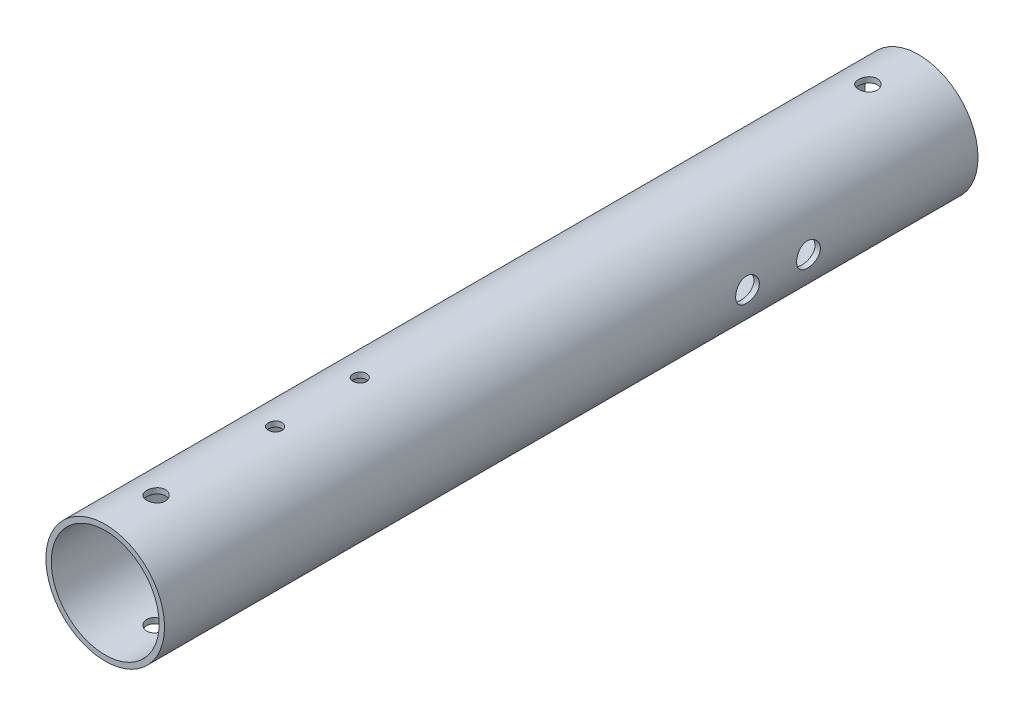
SolidWorks part; units mm, degrees
material "1060 Alloy"
ref_plane "Front Plane" through (0, 0, 0) normal (0, 0, 1) x (1, 0, 0)
ref_plane "Top Plane" through (0, 0, 0) normal (0, 1, 0) x (1, 0, 0)
ref_plane "Right Plane" through (0, 0, 0) normal (1, 0, 0) x (0, 0, -1)
sketch "Sketch2" plane through (0, 0, 0) normal (0, 0, 1) x (1, 0, 0)
  circle A0 centre (0, 0) radius 17.5
  circle A1 centre (0, 0) radius 15.9125
  dimension "D1" = 35
  dimension "D2" = 31.825
extrude "Boss-Extrude1" add sketch "Sketch2" along normal mid plane 240
sketch "Sketch4" plane through (0, 0, 0) normal (0, 1, 0) x (1, 0, 0)
  line L0 (0, 120) -> (0, 105) construction
  line L1 (15.9125, 120) -> (-15.9125, 120) construction
  dimension "D1" = 15
hole_wizard "M5 Clearance Hole1" positions "Sketch5" profile "Sketch6" hole size "M5" standard "AS"
sketch "Sketch5" plane through (0, 0, 0) normal (0, 1, 0) x (1, 0, 0)
  point P0 (0, 105)
sketch "Sketch6" plane through (0, 0, -105) normal (1, 0, 0) x (0, 0, -1)
  line L0 (0, 0) -> (0, 17.5)
  line L1 (0, 17.5) -> (2.75, 17.5)
  line L2 (2.75, 17.5) -> (2.75, 0)
  line L5 (2.75, 0) -> (0, 0)
  line L11 (0, -6.35) -> (0, 107.95) construction
  dimension "Thru Hole Dia." = 5.5
  dimension "Thru Hole Depth" = 17.5
mirror "Mirror1" about plane through (0, 0, 0) normal (0, 0, 1) of "M5 Clearance Hole1" second plane through (0, 0, 0) second plane normal (0, 1, 0)
sketch "Sketch7" plane through (0, 0, 0) normal (1, 0, 0) x (0, 0, -1)
  line L0 (52, 0) -> (70, 0) construction
  line L1 (70, 0) -> (120, 0) construction
  line L2 (120, -17.5) -> (120, 17.5) construction
  circle A0 centre (52, 0) radius 3.5
  circle A1 centre (70, 0) radius 3.5
  point P0 (70, 0)
  point P1 (52, 0)
  dimension "D3" = 7
  dimension "D1" = 18
  dimension "D2" = 50
extrude "Cut-Extrude1" cut sketch "Sketch7" against normal through all both and the other way through all
sketch "Sketch8" plane through (0, 0, 0) normal (0, 1, 0) x (1, 0, 0)
  circle A0 centre (0, -69.915) radius 2
  circle A1 centre (0, -69.915) radius 2 construction
  circle A2 centre (0, -44.915) radius 2
extrude "Cut-Extrude2" cut sketch "Sketch8" against normal through all both and the other way through all
equation "\"frontTubeLength\"= 1200mm"
equation "\"outDiameter\"= 35mm"
equation "\"keelOutDiameter\"= 1in"
equation "\"bottomTubeLength\"= \"frontTubeLength\"*0.9"
equation "\"D1@Sketch2\"=\"outDiameter\""
equation "\"D2@Sketch2\"=\"outDiameter\"-0.125in"
equation "\"D1@Boss-Extrude1\"=\"frontTubeLength\"*0.2"
